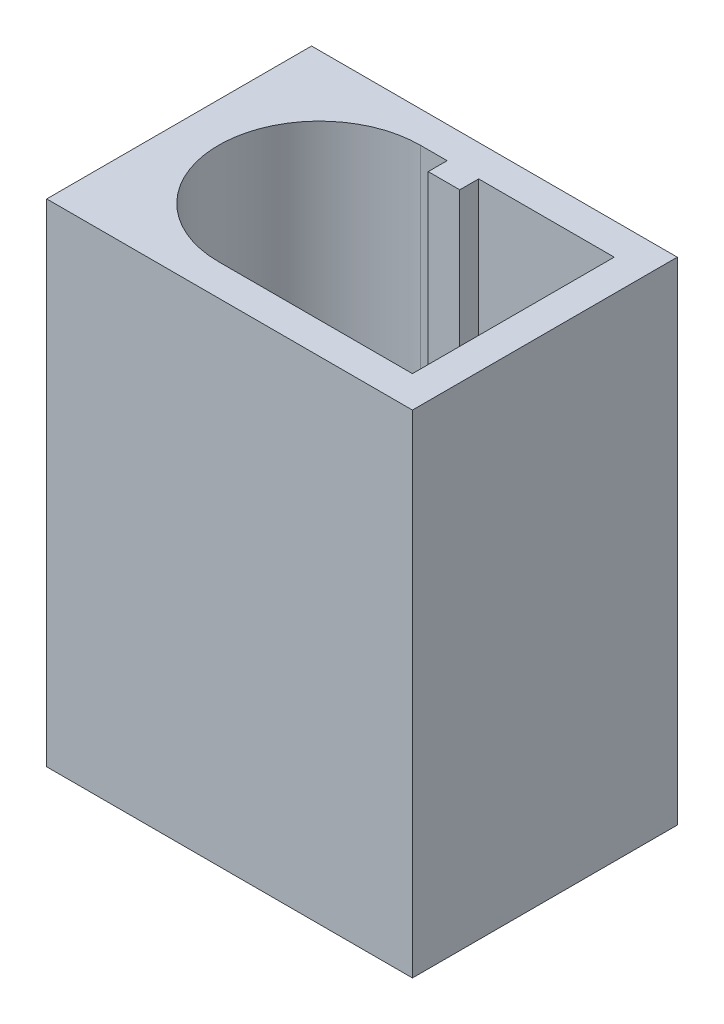
SolidWorks part; units mm, degrees
material "PE High Density"
ref_plane "Front Plane" through (0, 0, 0) normal (0, 0, 1) x (1, 0, 0)
ref_plane "Top Plane" through (0, 0, 0) normal (0, 1, 0) x (1, 0, 0)
ref_plane "Right Plane" through (0, 0, 0) normal (1, 0, 0) x (0, 0, -1)
sketch "Sketch1" plane through (0, 0, 0) normal (0, 1, 0) x (1, 0, 0)
  line L1 (0, 0) -> (5.8, 0)
  line L2 (0, 0) -> (0, 4.2)
  line L3 (0, 4.2) -> (5.8, 4.2)
  line L4 (5.8, 0) -> (5.8, 4.2)
  line L5 (2.9, 4.2) -> (2.9, 0) construction
  line L6 (0, 2.1) -> (5.8, 2.1) construction
  point P136 (2.9, 2.1)
  dimension "D1" = 5.8
  dimension "D2" = 4.2
extrude "Boss-Extrude1" add sketch "Sketch1" along normal blind 7.8
sketch "Sketch2" plane through (0, 7.8, 0) normal (0, 1, 0) x (1, 0, 0)
  line L0 (2.225, 0.5) -> (5.3, 0.5)
  line L1 (5.3, 0.5) -> (5.3, 3.7)
  line L2 (5.3, 3.7) -> (3.15, 3.7)
  line L3 (3.15, 3.7) -> (3.15, 3.4)
  line L4 (3.15, 3.4) -> (2.65, 3.4)
  line L5 (2.65, 3.4) -> (2.65, 3.7)
  line L6 (2.65, 3.7) -> (2.225, 3.7)
  line L7 (5.8, 0) -> (5.8, 4.2) construction
  line L8 (0, 0) -> (5.8, 0) construction
  line L9 (5.8, 4.2) -> (0, 4.2) construction
  line L10 (4.225, 3.7) -> (4.225, 0.5) construction
  line L11 (2.9, 3.4) -> (2.9, 4.2) construction
  arc A0 (2.225, 3.7) -> (2.225, 0.5) centre (2.225, 2.1) ccw
  point P19 (2.6689, 3.3838)
  dimension "D1" = 0.5
  dimension "D2" = 0.5
  dimension "D3" = 0.5
  dimension "D4" = 2
  dimension "D5" = 0.5
  dimension "D6" = 0.3
extrude "Cut-Extrude1" cut sketch "Sketch2" against normal blind 7
